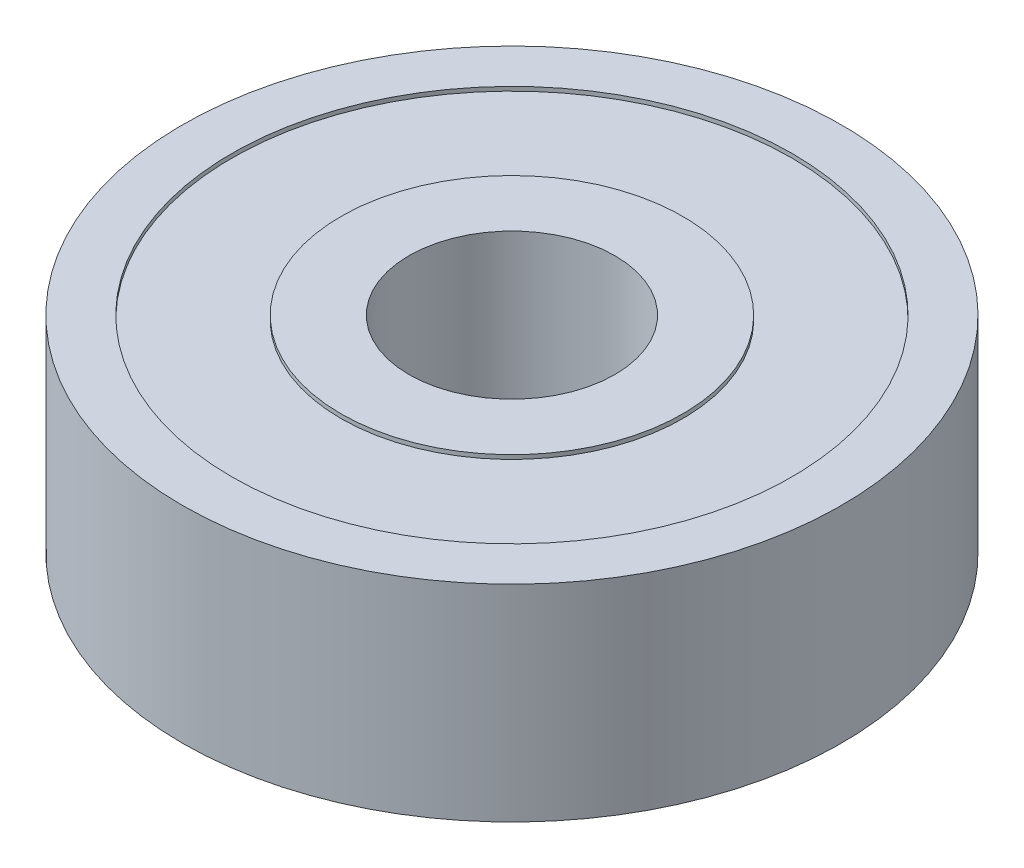
SolidWorks part; units mm, degrees
ref_plane "Front Plane" through (0, 0, 0) normal (0, 0, 1) x (1, 0, 0)
ref_plane "Top Plane" through (0, 0, 0) normal (0, 1, 0) x (1, 0, 0)
ref_plane "Right Plane" through (0, 0, 0) normal (1, 0, 0) x (0, 0, -1)
sketch "Sketch1" plane through (0, 0, 0) normal (0, 1, 0) x (1, 0, 0)
  circle A0 centre (0, 0) radius 8
  circle A1 centre (0, 0) radius 2.5
  dimension "D1" = 16
  dimension "D2" = 5
extrude "Boss-Extrude1" add sketch "Sketch1" along normal blind 5
sketch "Sketch2" plane through (0, 5, 0) normal (0, 1, 0) x (1, 0, 0)
  circle A0 centre (0, 0) radius 4.15
  circle A1 centre (0, 0) radius 6.8
  dimension "D1" = 8.3
  dimension "D2" = 13.6
extrude "Cut-Extrude1" cut sketch "Sketch2" against normal blind 0.1
sketch "Sketch3" plane through (0, 0, 0) normal (0, -1, 0) x (1, 0, 0)
  circle A0 centre (0, 0) radius 4.15 construction
  circle A1 centre (0, 0) radius 6.8
  circle A2 centre (0, 0) radius 6.8
  circle A3 centre (0, 0) radius 4.15
  dimension "D1" = 0
extrude "Cut-Extrude2" cut sketch "Sketch3" against normal blind 0.1
